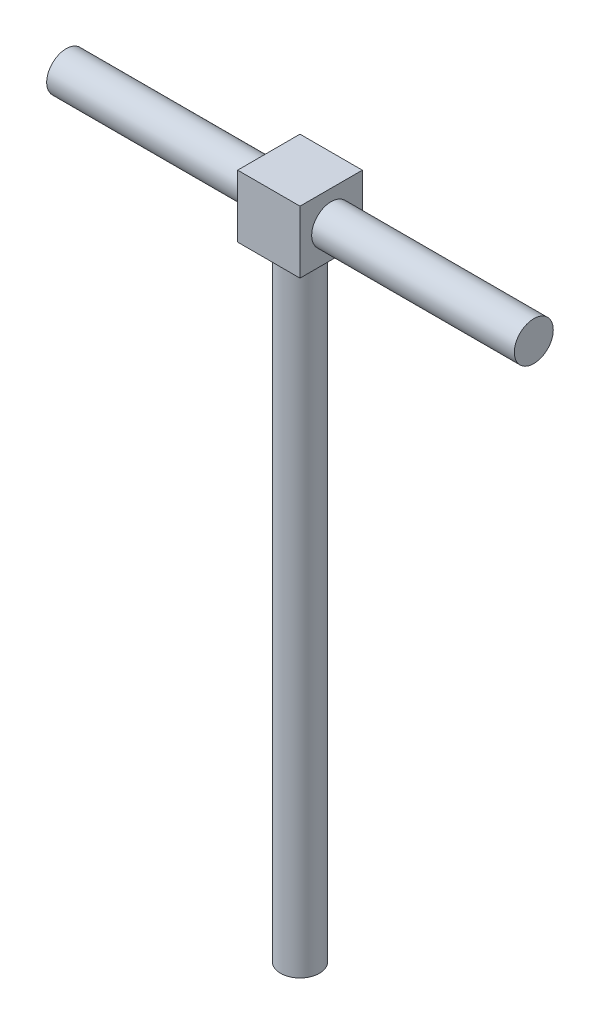
SolidWorks part; units mm, degrees
ref_plane "Front Plane" through (0, 0, 0) normal (0, 0, 1) x (1, 0, 0)
ref_plane "Top Plane" through (0, 0, 0) normal (0, 1, 0) x (1, 0, 0)
ref_plane "Right Plane" through (0, 0, 0) normal (1, 0, 0) x (0, 0, -1)
sketch "Sketch1" plane through (0, 0, 0) normal (0, 1, 0) x (1, 0, 0)
  circle A0 centre (0, 0) radius 2.5
  dimension "D1" = 5
extrude "Boss-Extrude1" add sketch "Sketch1" along normal blind 80
sketch "Sketch2" plane through (0, 80, 0) normal (0, 1, 0) x (1, 0, 0)
  line L1 (-4, -4) -> (4, -4)
  line L2 (-4, -4) -> (-4, 4)
  line L3 (-4, 4) -> (4, 4)
  line L4 (4, -4) -> (4, 4)
  line L5 (-4, -4) -> (4, 4) construction
  line L6 (-4, 4) -> (4, -4) construction
  point P0 (0, 0)
  dimension "D1" = 8
  dimension "D2" = 8
extrude "Boss-Extrude2" add sketch "Sketch2" along normal blind 8
sketch "Sketch3" plane through (0, 0, 0) normal (1, 0, 0) x (0, 0, -1)
  line L0 (0, 4.4) -> (0, -4.4) construction
  line L1 (-4, 88) -> (4, 88) construction
  circle A0 centre (0, 84) radius 2.5
  point P4 (0, 0)
  point P7 (0, 0)
  dimension "D2" = 5
  dimension "D1" = 4
extrude "Boss-Extrude3" add sketch "Sketch3" along normal mid plane 60
